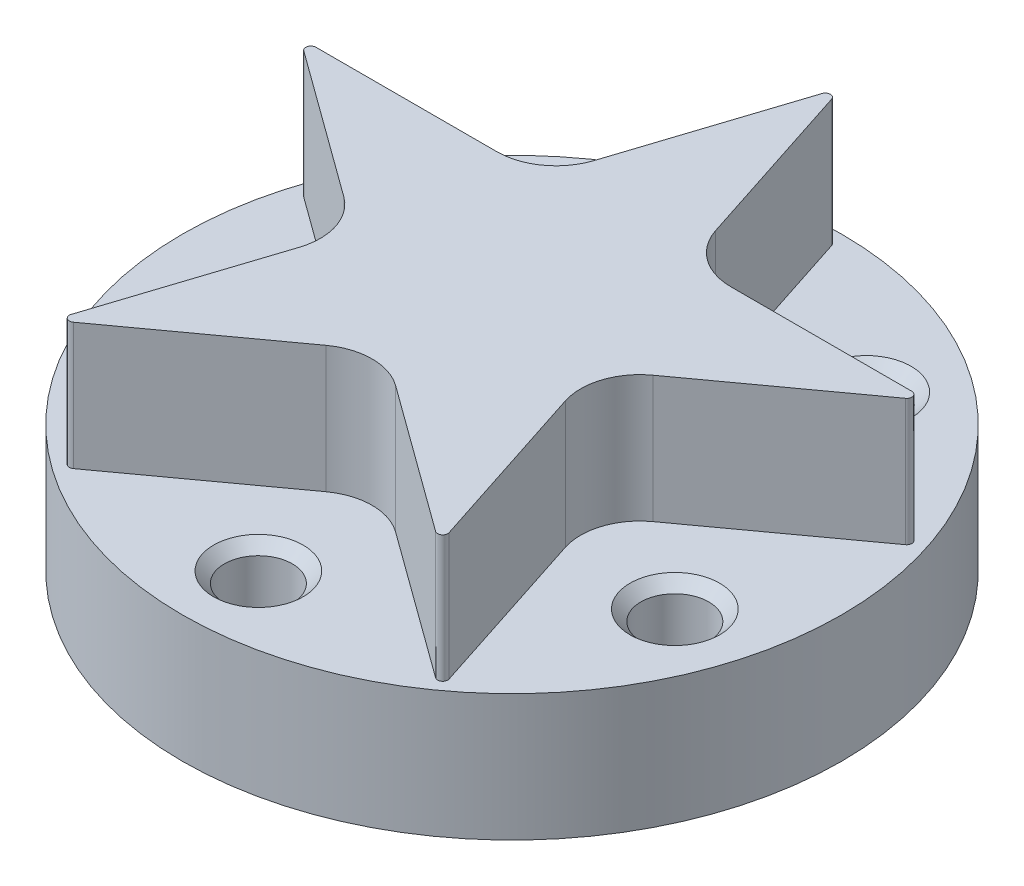
SolidWorks part; units mm, degrees
ref_plane "Front Plane" through (0, 0, 0) normal (0, 0, 1) x (1, 0, 0)
ref_plane "Top Plane" through (0, 0, 0) normal (0, 1, 0) x (1, 0, 0)
ref_plane "Right Plane" through (0, 0, 0) normal (1, 0, 0) x (0, 0, -1)
sketch "Sketch1" plane through (0, 0, 0) normal (0, 1, 0) x (1, 0, 0)
  circle A0 centre (0, 0) radius 24.765
  dimension "D1" = 49.53
extrude "Boss-Extrude1" add sketch "Sketch1" along normal blind 19.05
sketch "Sketch2" plane through (0, 19.05, 0) normal (0, 1, 0) x (1, 0, 0)
  line L0 (-14.1941, -18.9201) -> (-9.9944, -5.9945)
  line L6 (0.3624, 23.6498) -> (4.5621, 10.7242)
  line L7 (13.6079, -19.3461) -> (2.6127, -11.3576)
  line L8 (-22.3803, 7.6528) -> (-8.7896, 7.6528)
  line L9 (22.6043, 6.9636) -> (11.6091, -1.0249)
  line L10 (0, 0) -> (0, 24.765) construction
  line L11 (-14.5565, -20.0353) -> (14.5565, -20.0353) construction
  line L12 (14.5565, -20.0353) -> (23.5529, 7.6528) construction
  line L13 (23.5529, 7.6528) -> (0, 24.765) construction
  line L14 (0, 24.765) -> (-23.5529, 7.6528) construction
  line L15 (-23.5529, 7.6528) -> (-14.5565, -20.0353) construction
  line L16 (-4.5621, 10.7242) -> (-0.3624, 23.6498)
  line L17 (-8.9964, -2.9231) -> (-5.5601, 7.6528) construction
  line L18 (8.7896, 7.6528) -> (22.3803, 7.6528)
  line L19 (-5.5601, 7.6528) -> (0, 7.6528) construction
  line L20 (0, 7.6528) -> (5.5601, 7.6528) construction
  line L21 (9.9944, -5.9945) -> (14.1941, -18.9201)
  line L22 (5.5601, 7.6528) -> (8.9964, -2.9231) construction
  line L23 (-2.6127, -11.3576) -> (-13.6079, -19.3461)
  line L24 (8.9964, -2.9231) -> (0, -9.4594) construction
  line L25 (-11.6091, -1.0249) -> (-22.6043, 6.9636)
  line L26 (0, -9.4594) -> (-8.9964, -2.9231) construction
  circle A0 centre (0, 0) radius 24.765 construction
  arc A1 (-4.5621, 10.7242) -> (-8.7896, 7.6528) centre (-8.7896, 12.0978) cw
  arc A2 (4.5621, 10.7242) -> (8.7896, 7.6528) centre (8.7896, 12.0978) ccw
  arc A3 (11.6091, -1.0249) -> (9.9944, -5.9945) centre (14.2218, -4.621) ccw
  arc A4 (2.6127, -11.3576) -> (-2.6127, -11.3576) centre (0, -14.9537) ccw
  arc A5 (-9.9944, -5.9945) -> (-11.6091, -1.0249) centre (-14.2218, -4.621) ccw
  arc A6 (-14.1941, -18.9201) -> (-13.6079, -19.3461) centre (-13.8318, -19.0378) ccw
  arc A7 (13.6079, -19.3461) -> (14.1941, -18.9201) centre (13.8318, -19.0378) ccw
  arc A8 (22.6043, 6.9636) -> (22.3803, 7.6528) centre (22.3803, 7.2718) ccw
  arc A9 (0.3624, 23.6498) -> (-0.3624, 23.6498) centre (0, 23.5321) ccw
  arc A10 (-22.3803, 7.6528) -> (-22.6043, 6.9636) centre (-22.3803, 7.2718) ccw
  dimension "D1" = 4.445
  dimension "D2" = 0.381
extrude "Cut-Extrude1" cut sketch "Sketch2" against normal blind 9.525 flip side to cut
sketch "Sketch3" plane through (0, 9.525, 0) normal (0, 1, 0) x (1, 0, 0)
  line L0 (0, 0) -> (0, -19.05) construction
  line L1 (0, -19.05) -> (18.1176, -5.8868) construction
  line L2 (18.1176, -5.8868) -> (11.1973, 15.4118) construction
  line L3 (11.1973, 15.4118) -> (-11.1973, 15.4118) construction
  line L4 (-11.1973, 15.4118) -> (-18.1176, -5.8868) construction
  line L5 (-18.1176, -5.8868) -> (0, -19.05) construction
  circle A0 centre (0, 0) radius 19.05 construction
  circle A1 centre (-11.1973, 15.4118) radius 2.5527
  circle A2 centre (11.1973, 15.4118) radius 2.5527
  circle A3 centre (18.1176, -5.8868) radius 2.5527
  circle A4 centre (0, -19.05) radius 2.5527
  circle A5 centre (-18.1176, -5.8868) radius 2.5527
  point P20 (0, 0)
  dimension "D1" = 38.1
  dimension "D2" = 5.1054
  dimension "D3" = 5
hole_wizard "1/4-20 Tapped Hole5" positions "Sketch6" profile "Sketch8" tap size "1/4-20" standard "ANSI Inch"
sketch "Sketch6" plane through (0, 9.525, 0) normal (0, 1, 0) x (1, 0, 0)
  point P0 (-18.1176, -5.8868)
  point P3 (-11.1973, 15.4118)
  point P6 (11.1973, 15.4118)
  point P9 (18.1176, -5.8868)
  point P12 (0, -19.05)
sketch "Sketch8" plane through (-18.1176, 9.525, 5.8868) normal (1, 0, 0) x (0, 0, 1)
  line L0 (0, 0) -> (0, 9.1538)
  line L1 (0, 9.1538) -> (2.5527, 7.62)
  line L2 (2.5527, 7.62) -> (2.5527, 0.8128)
  line L3 (2.5527, 0.8128) -> (3.3655, 0)
  line L5 (3.3655, 0) -> (0, 0)
  line L6 (-2.5527, 0.8128) -> (-3.3655, 0) construction
  line L10 (0, 9.1538) -> (-2.5527, 7.62) construction
  line L11 (0, -6.35) -> (0, 107.95) construction
  dimension "Tap Drill Dia." = 5.1054
  dimension "Tap Drill Depth" = 7.62
  dimension "Near C'Sink Dia." = 6.731
  dimension "Near C'Sink Angle" = 90
  dimension "Drill Angle" = 118
cosmetic thread "Hole Thread1" parameters "D1"=6.985, "D2"=6.35
cosmetic thread "Hole Thread2" parameters "D1"=6.985, "D2"=6.35
cosmetic thread "Hole Thread3" parameters "D1"=6.985, "D2"=6.35
cosmetic thread "Hole Thread4" parameters "D1"=6.985, "D2"=6.35
cosmetic thread "Hole Thread5" parameters "D1"=6.985, "D2"=6.35
sketch "Sketch9" plane through (0, 19.05, 0) normal (0, 1, 0) x (1, 0, 0)
  line L0 (-1.2192, 2.6968) -> (1.7484, -3.9234)
  line L1 (1.7484, -3.9234) -> (2.7721, -3.9234)
  line L2 (2.7721, -3.9234) -> (-0.1955, 2.6968)
  line L3 (-0.1955, 2.6968) -> (-1.2192, 2.6968)
  line L4 (-2.5868, 0.8211) -> (-0.3701, -3.9234)
  line L5 (-0.3701, -3.9234) -> (0.6512, -3.9234)
  line L6 (0.6512, -3.9234) -> (-1.5655, 0.8211)
  line L7 (-1.5655, 0.8211) -> (-2.5868, 0.8211)
  line L8 (4.842, -3.9234) -> (1.0793, 4.5489)
  line L9 (1.0793, 4.5489) -> (0.0549, 4.5489)
  line L10 (0.0549, 4.5489) -> (3.8175, -3.9234)
  line L11 (3.8175, -3.9234) -> (4.842, -3.9234)
  line L12 (-3.5257, -1.3064) -> (-2.3893, -3.9234)
  line L13 (-2.3893, -3.9234) -> (-1.3638, -3.9234)
  line L14 (-1.3638, -3.9234) -> (-2.5002, -1.3064)
  line L15 (-2.5002, -1.3064) -> (-3.5257, -1.3064)
  line L16 (-4.7466, -2.8595) -> (-4.3442, -3.9234)
  line L17 (-4.3442, -3.9234) -> (-3.3115, -3.9234)
  line L18 (-3.3115, -3.9234) -> (-3.7904, -2.8595)
  line L19 (-3.7904, -2.8595) -> (-4.7466, -2.8595)
  line L20 (-3.3115, -3.9234) -> (-2.3893, -3.9234) construction
  line L21 (-1.3638, -3.9234) -> (-0.3701, -3.9234) construction
  line L22 (0.6512, -3.9234) -> (1.7484, -3.9234) construction
  line L23 (2.7721, -3.9234) -> (3.8175, -3.9234) construction
  line L24 (-4.3442, -3.9234) -> (-7.6981, -3.9234) construction
  line L25 (4.842, -3.9234) -> (7.7417, -3.9234) construction
  circle A0 centre (0, 0) radius 10.1118 construction
  spline S0 degree 3 poles (0.0219, -8.7019) (-4.7351, -8.7019) (-8.6049, -4.832) (-8.6048, -0.0753) knots 0 0 0 0 1 1 1 1
  spline S1 degree 3 poles (-8.6048, -0.0753) (-8.6048, 4.6816) (-4.735, 8.5514) (0.0219, 8.5514) knots 0 0 0 0 1 1 1 1
  spline S2 degree 3 poles (0.0219, 8.5514) (4.7788, 8.5514) (8.6484, 4.6815) (8.6484, -0.0754) knots 0 0 0 0 1 1 1 1
  spline S3 degree 3 poles (8.6484, -0.0754) (8.6484, -4.8321) (4.7788, -8.7019) (0.0219, -8.7019) knots 0 0 0 0 1 1 1 1
  spline S4 degree 3 poles (0.0219, 9.3451) (-5.1727, 9.3451) (-9.3986, 5.1192) (-9.3986, -0.0754) knots 0 0 0 0 1 1 1 1
  spline S5 degree 3 poles (-9.3986, -0.0754) (-9.3986, -5.2697) (-5.1727, -9.4956) (0.0219, -9.4956) knots 0 0 0 0 1 1 1 1
  spline S6 degree 3 poles (0.0219, -9.4956) (5.2165, -9.4956) (9.4421, -5.2697) (9.4421, -0.0754) knots 0 0 0 0 1 1 1 1
  spline S7 degree 3 poles (9.4421, -0.0754) (9.4421, 5.1192) (5.2165, 9.3451) (0.0219, 9.3451) knots 0 0 0 0 1 1 1 1
